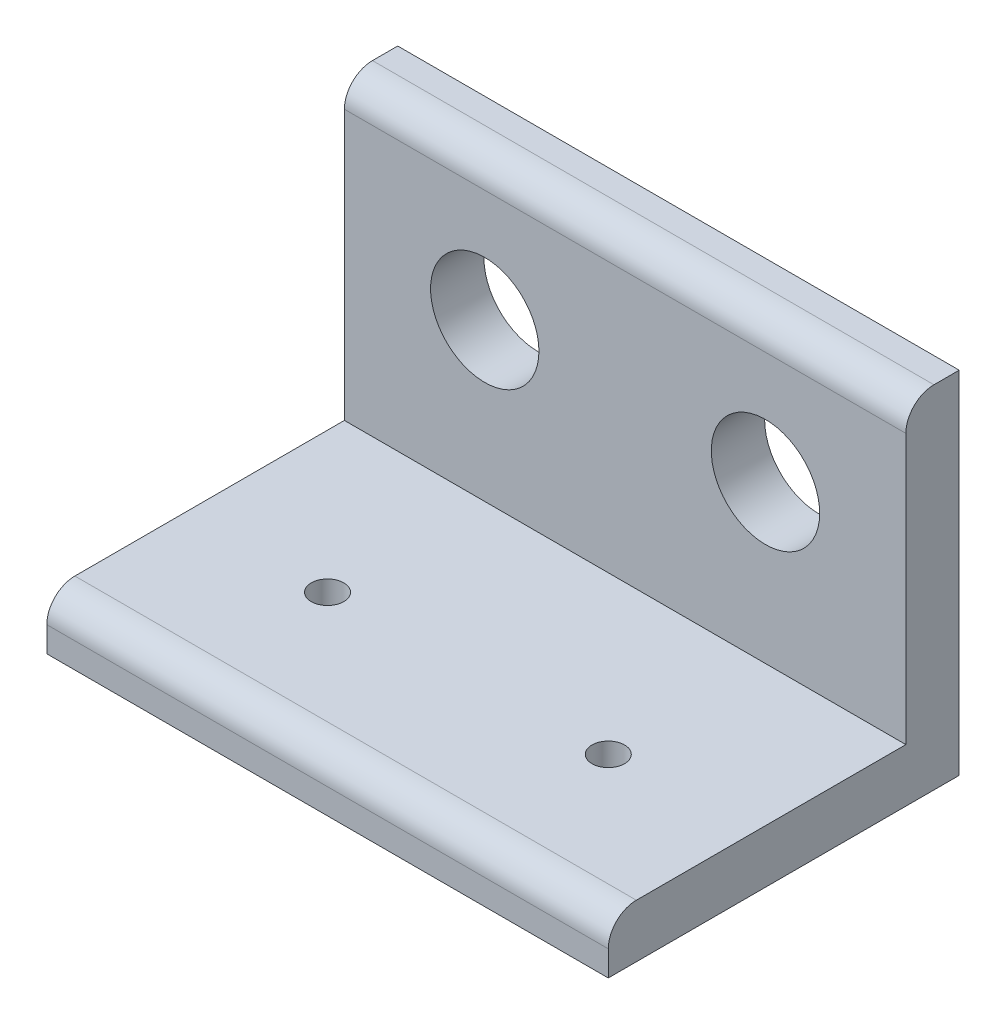
SolidWorks part; units mm, degrees
ref_plane "Front Plane" through (0, 0, 0) normal (0, 0, 1) x (1, 0, 0)
ref_plane "Top Plane" through (0, 0, 0) normal (0, 1, 0) x (1, 0, 0)
ref_plane "Right Plane" through (0, 0, 0) normal (1, 0, 0) x (0, 0, -1)
sketch "Sketch2" plane through (0, 0, 0) normal (1, 0, 0) x (0, 0, -1)
  line L0 (0, 0) -> (31.75, 0)
  line L1 (31.75, 0) -> (31.75, 31.75)
  line L2 (31.75, 31.75) -> (26.924, 31.75)
  line L3 (26.924, 31.75) -> (26.924, 4.826)
  line L4 (26.924, 4.826) -> (0, 4.826)
  line L5 (0, 4.826) -> (0, 0)
  dimension "D1" = 31.75
  dimension "D2" = 31.75
  dimension "D3" = 4.826
  dimension "D4" = 4.826
extrude "Boss-Extrude1" add sketch "Sketch2" against normal blind 50.8
sketch "Sketch3" plane through (0, 0, -26.924) normal (0, 0, 1) x (1, 0, 0)
  line L0 (-50.8, 0) -> (0, 0) construction
  line L1 (-50.8, 31.75) -> (-50.8, 4.826) construction
  circle A0 centre (-38.1, 19.05) radius 4.9022
  circle A1 centre (-12.7, 19.05) radius 4.9022
  dimension "D1" = 9.8044
  dimension "D2" = 19.05
  dimension "D3" = 12.7
  dimension "D4" = 38.1
extrude "Cut-Extrude1" cut sketch "Sketch3" against normal blind 50.8
sketch "Sketch4" plane through (0, 4.826, 0) normal (0, 1, 0) x (1, 0, 0)
  line L0 (-50.8, 31.75) -> (0, 31.75) construction
  line L1 (-50.8, 26.924) -> (-50.8, 0) construction
  circle A0 centre (-38.1, 12.7) radius 1.4732
  circle A1 centre (-12.7, 12.7) radius 1.4732
  dimension "D1" = 2.9464
  dimension "D2" = 19.05
  dimension "D3" = 12.7
  dimension "D4" = 38.1
extrude "Cut-Extrude2" cut sketch "Sketch4" against normal blind 50.8
fillet "Fillet1" radius 2.54 2 edges at (-25.4, 4.826, 0) (-25.4, 31.75, -26.924)
